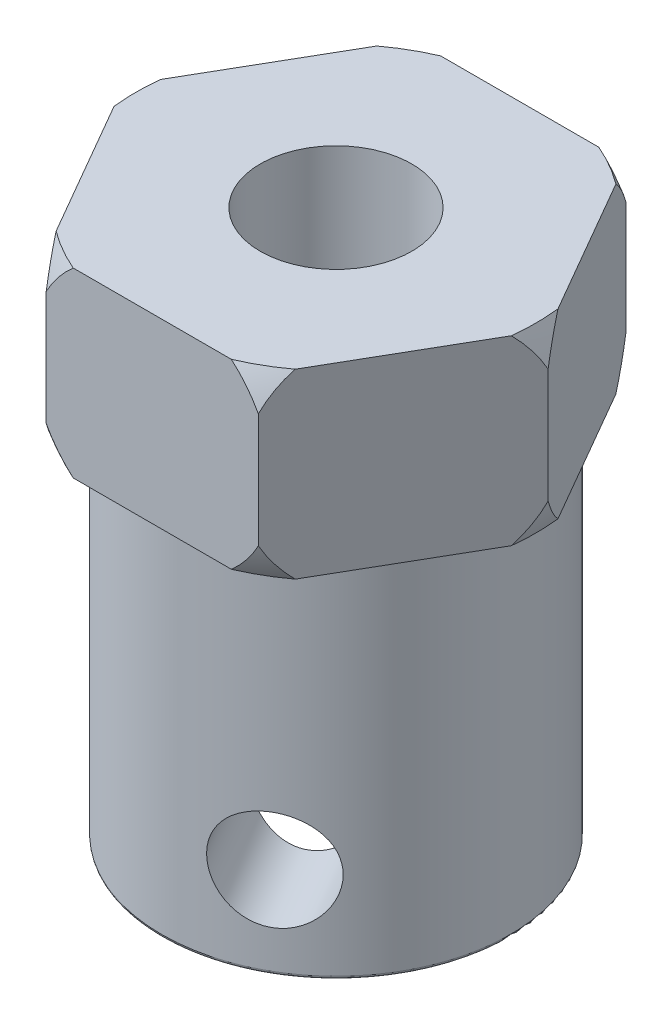
SolidWorks part; units mm, degrees
ref_plane "前视基准面" through (0, 0, 0) normal (0, 0, 1) x (1, 0, 0)
ref_plane "上视基准面" through (0, 0, 0) normal (0, 1, 0) x (1, 0, 0)
ref_plane "右视基准面" through (0, 0, 0) normal (1, 0, 0) x (0, 0, -1)
sketch "草图1" plane through (0, 0, 0) normal (0, 1, 0) x (1, 0, 0)
  line L1 (-3.5, -6.0622) -> (3.5, -6.0622)
  line L2 (3.5, -6.0622) -> (7, 0)
  line L3 (7, 0) -> (3.5, 6.0622)
  line L4 (3.5, 6.0622) -> (-3.5, 6.0622)
  line L5 (-3.5, 6.0622) -> (-7, 0)
  line L6 (-7, 0) -> (-3.5, -6.0622)
  circle A0 centre (0, 0) radius 6.0622 construction
  dimension "D1" = 7
extrude "凸台-拉伸1" add sketch "草图1" along normal blind 6
sketch "草图2" plane through (0, 0, 0) normal (0, -1, 0) x (1, 0, 0)
  circle A0 centre (0, 0) radius 5.75
  dimension "D1" = 11.5
extrude "凸台-拉伸2" add sketch "草图2" along normal blind 12
sketch "草图3" plane through (0, 6, 0) normal (0, 1, 0) x (1, 0, 0)
  circle A0 centre (0, 0) radius 2.5
  dimension "D1" = 5
extrude "切除-拉伸1" cut sketch "草图3" against normal blind 29
sketch "草图4" plane through (0, 0, 0) normal (0, 0, 1) x (1, 0, 0)
  line L0 (-3.5, 0) -> (3.5, 0) construction
  line L2 (-7, 0) -> (-3.5, 0) construction
  line L3 (-7, 6) -> (-7, 0) construction
  line L4 (-7, 6) -> (-3.5, 6) construction
  line L5 (-7, 0) -> (-6.6002, 0)
  line L6 (-7, 6) -> (-7, 4.8875)
  line L7 (-7, 6) -> (-6.6002, 6)
  line L8 (-7, 1.1125) -> (-7, 0)
  arc A0 (-6.6002, 6) -> (-7, 4.8875) centre (0, 3) ccw
  arc A1 (-7, 1.1125) -> (-6.6002, 0) centre (0, 3) ccw
  dimension "D3" = 14.5
  dimension "D1" = 3
  dimension "D2" = 7
revolve "切除-旋转1" cut sketch "草图4" angle 360 about axis through (0, -23, 0) along (0, 1, 0)
ref_plane "基准面1" through (1.75, 0, 3.0311) normal (0.5, 0, 0.866) x (0.866, 0, -0.5)
sketch "草图5" plane through (1.75, 0, 3.0311) normal (0.5, 0, 0.866) x (0.866, 0, -0.5)
  line L0 (-5.75, -12) -> (5.75, -12) construction
  circle A0 centre (0, -9) radius 1.65
  dimension "D1" = 3.3
  dimension "D2" = 3
extrude "切除-拉伸2" cut sketch "草图5" against normal mid plane 7
fillet "圆角2" radius 0.1 2 edges at (0, -12, -2.5) (0, -12, -5.75)
